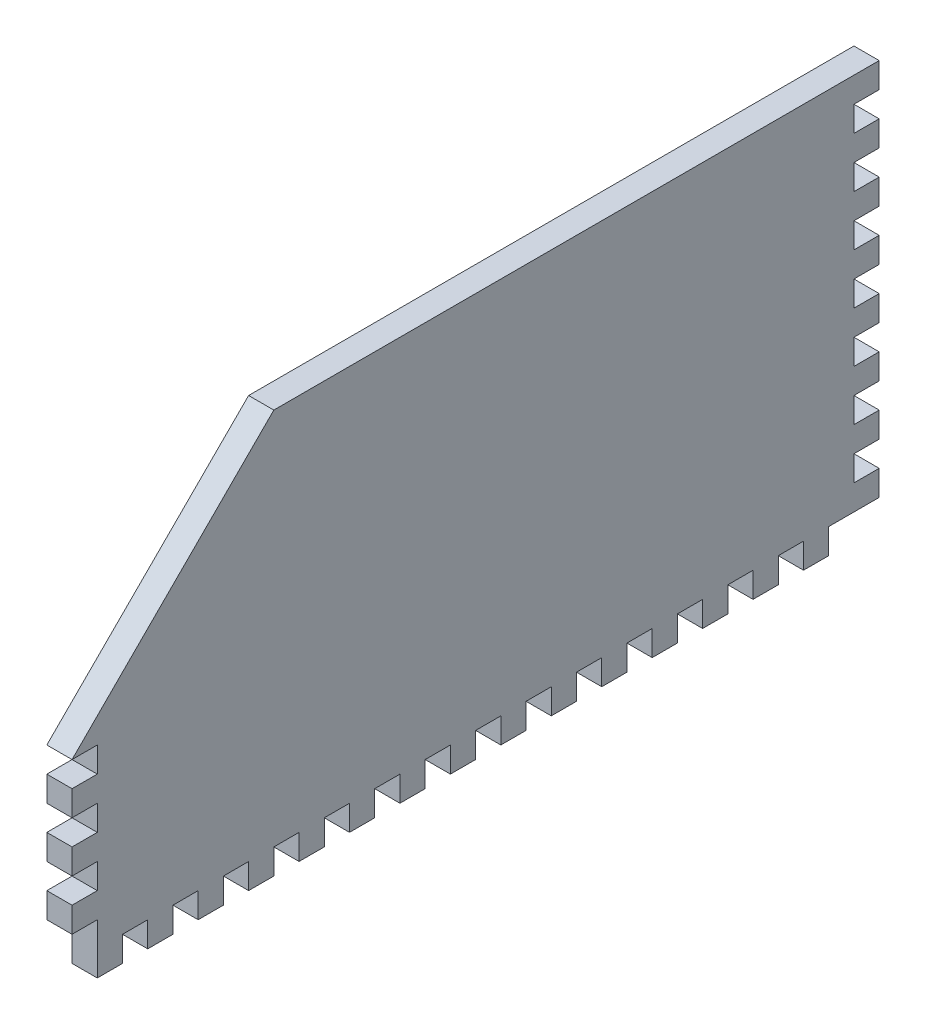
SolidWorks part; units mm, degrees
ref_plane "Front Plane" through (0, 0, 0) normal (0, 0, 1) x (1, 0, 0)
ref_plane "Top Plane" through (0, 0, 0) normal (0, 1, 0) x (1, 0, 0)
ref_plane "Right Plane" through (0, 0, 0) normal (1, 0, 0) x (0, 0, -1)
sketch "Sketch1" plane through (0, 0, 0) normal (1, 0, 0) x (0, 0, -1)
  line L1 (0, 0) -> (203.2, 0)
  line L2 (0, 0) -> (0, 101.6)
  line L3 (0, 101.6) -> (203.2, 101.6)
  line L4 (203.2, 0) -> (203.2, 101.6)
  dimension "D1" = 203.2
  dimension "D2" = 101.6
extrude "Boss-Extrude1" add sketch "Sketch1" against normal blind 6.35 contours L3 L4 L1 L2
sketch "Sketch2" plane through (0, 0, 0) normal (0, -1, 0) x (1, 0, 0)
  line L0 (-6.35, 0) -> (-6.35, -203.2) construction
  line L1 (0, -203.2) -> (-6.35, -203.2)
  line L2 (0, -203.2) -> (0, -190.5)
  line L3 (0, -190.5) -> (-6.35, -190.5)
  line L4 (-6.35, -203.2) -> (-6.35, -190.5)
extrude "Cut-Extrude1" cut sketch "Sketch2" against normal blind 6.35
sketch "Sketch5" plane through (0, 0, 0) normal (0, -1, 0) x (1, 0, 0)
  line L0 (0, 0) -> (0, -190.5) construction
  line L1 (0, -184.15) -> (-6.35, -184.15)
  line L2 (0, -184.15) -> (0, -177.8)
  line L3 (0, -177.8) -> (-6.35, -177.8)
  line L4 (-6.35, -184.15) -> (-6.35, -177.8)
  line L5 (-6.35, 0) -> (-6.35, -190.5) construction
extrude "Cut-Extrude2" cut sketch "Sketch5" against normal blind 6.35
pattern_linear "LPattern1" count 15 spacing 12.7 along (0, 0, 1) of "Cut-Extrude2"
sketch "Sketch6" plane through (0, 0, -203.2) normal (0, 0, -1) x (-1, 0, 0)
  line L0 (0, 6.35) -> (0, 101.6) construction
  line L1 (0, 12.7) -> (6.35, 12.7)
  line L2 (0, 12.7) -> (0, 19.05)
  line L3 (0, 19.05) -> (6.35, 19.05)
  line L4 (6.35, 12.7) -> (6.35, 19.05)
  line L5 (6.35, 6.35) -> (6.35, 101.6) construction
extrude "Cut-Extrude3" cut sketch "Sketch6" against normal blind 6.35
pattern_linear "LPattern2" count 7 spacing 12.7 along (0, 1, 0) of "Cut-Extrude3"
sketch "Sketch7" plane through (0, 0, 0) normal (1, 0, 0) x (0, 0, -1)
  line L0 (0, 101.6) -> (0, 50.8)
  line L1 (0, 6.35) -> (0, 101.6) construction
  line L2 (0, 50.8) -> (50.8, 101.6)
  line L3 (0, 101.6) -> (203.2, 101.6) construction
  line L4 (50.8, 101.6) -> (0, 101.6)
  dimension "D1" = 50.8
  dimension "D2" = 50.8
extrude "Cut-Extrude4" cut sketch "Sketch7" against normal blind 6.35
sketch "Sketch8" plane through (0, 0, 0) normal (0, 0, 1) x (1, 0, 0)
  line L0 (0, 6.35) -> (-6.35, 6.35) construction
  line L1 (0, 6.35) -> (-6.35, 6.35)
  line L2 (0, 6.35) -> (0, 12.7)
  line L3 (0, 12.7) -> (-6.35, 12.7)
  line L4 (-6.35, 6.35) -> (-6.35, 12.7)
  line L5 (-6.35, 6.35) -> (-6.35, 50.8) construction
extrude "Cut-Extrude5" cut sketch "Sketch8" against normal blind 6.35
sketch "Sketch10" plane through (0, 0, 0) normal (0, 0, 1) x (1, 0, 0)
  line L0 (-6.35, 12.7) -> (-6.35, 50.8) construction
  line L1 (-6.35, 19.05) -> (0, 19.05)
  line L2 (-6.35, 19.05) -> (-6.35, 25.4)
  line L3 (-6.35, 25.4) -> (0, 25.4)
  line L4 (0, 19.05) -> (0, 25.4)
  line L5 (0, 12.7) -> (0, 50.8) construction
extrude "Cut-Extrude6" cut sketch "Sketch10" against normal blind 6.35
pattern_linear "LPattern3" count 3 spacing 12.7 along (0, 1, 0) of "Cut-Extrude6"
